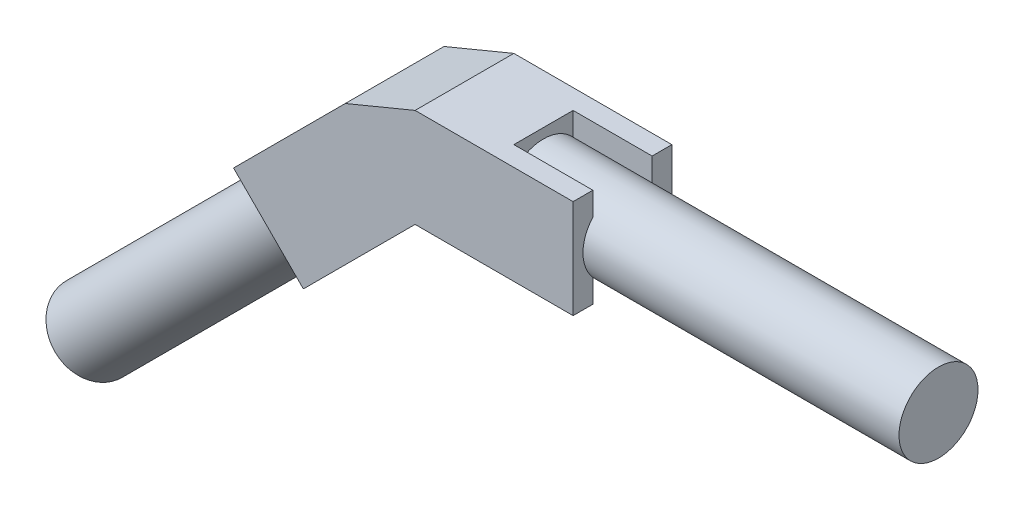
SolidWorks part; units mm, degrees
ref_plane "Front Plane" through (0, 0, 0) normal (0, 0, 1) x (1, 0, 0)
ref_plane "Top Plane" through (0, 0, 0) normal (0, 1, 0) x (1, 0, 0)
ref_plane "Right Plane" through (0, 0, 0) normal (1, 0, 0) x (0, 0, -1)
sketch "Sketch1" plane through (0, 0, 0) normal (1, 0, 0) x (0, 0, -1)
  circle A0 centre (0, 0) radius 12.7
  dimension "D1" = 25.4
extrude "Boss-Extrude1" add sketch "Sketch1" along normal blind 127
sketch "Sketch2" plane through (0, 0, 0) normal (-1, 0, 0) x (0, 0, 1)
  line L1 (-15.875, 15.875) -> (15.875, 15.875)
  line L2 (-15.875, 15.875) -> (-15.875, -15.875)
  line L3 (-15.875, -15.875) -> (15.875, -15.875)
  line L4 (15.875, 15.875) -> (15.875, -15.875)
  line L5 (-15.875, 15.875) -> (15.875, -15.875) construction
  line L6 (-15.875, -15.875) -> (15.875, 15.875) construction
  point P0 (0, 0)
  dimension "D1" = 31.75
  dimension "D2" = 31.75
extrude "Boss-Extrude2" add sketch "Sketch2" along normal blind 25.4
sketch "Sketch3" plane through (0, 0, 15.875) normal (0, 0, 1) x (1, 0, 0)
  line L1 (0, 15.875) -> (25.4, 15.875)
  line L2 (0, 15.875) -> (0, -15.875)
  line L3 (0, -15.875) -> (25.4, -15.875)
  line L4 (25.4, 15.875) -> (25.4, -15.875)
  dimension "D1" = 25.4
  dimension "D2" = 31.75
extrude "Boss-Extrude3" add sketch "Sketch3" against normal blind 6.35
sketch "Sketch4" plane through (0, 0, -15.875) normal (0, 0, -1) x (-1, 0, 0)
  line L1 (0, 15.875) -> (-25.4, 15.875)
  line L2 (0, 15.875) -> (0, -15.875)
  line L3 (0, -15.875) -> (-25.4, -15.875)
  line L4 (-25.4, 15.875) -> (-25.4, -15.875)
extrude "Boss-Extrude4" add sketch "Sketch4" against normal blind 6.35
ref_plane "Plane3" through (-20.6375, -20.6375, 0) normal (-0.7071, -0.7071, 0) x (0, 0, 1)
sketch "Sketch9" plane through (-20.6375, -20.6375, 0) normal (-0.7071, -0.7071, 0) x (0, 0, 1)
  line L1 (-15.875, 6.7352) -> (15.875, 6.7352)
  line L2 (-15.875, 6.7352) -> (-15.875, 38.4852)
  line L3 (-15.875, 38.4852) -> (15.875, 38.4852)
  line L4 (15.875, 6.7352) -> (15.875, 38.4852)
  dimension "D1" = 31.75
  dimension "D2" = 31.75
extrude "Boss-Extrude5" add sketch "Sketch9" along normal blind 25.4 separate body contours L3 L4 L1 L2
sketch "Sketch11" plane through (-38.598, -38.598, 0) normal (-0.7071, -0.7071, 0) x (0, 0, 1)
  line L0 (0, 38.4852) -> (0, 6.7352) construction
  line L1 (-15.875, 38.4852) -> (15.875, 38.4852) construction
  line L2 (-15.875, 6.7352) -> (15.875, 6.7352) construction
  line L3 (-15.875, 22.6102) -> (15.875, 22.6102) construction
  line L4 (-15.875, 6.7352) -> (-15.875, 38.4852) construction
  line L5 (15.875, 6.7352) -> (15.875, 38.4852) construction
  circle A0 centre (0, 22.6102) radius 12.7
  dimension "D1" = 25.4
extrude "Boss-Extrude6" add sketch "Sketch11" along normal blind 127
sketch "Sketch13" plane through (0, 0, 15.875) normal (0, 0, 1) x (1, 0, 0)
  line L0 (-43.3605, -33.8355) -> (-61.321, -51.796)
  line L1 (-61.321, -51.796) -> (-83.7717, -29.3454)
  line L4 (-83.7717, -29.3454) -> (-65.8112, -11.3849)
  line L5 (-65.8112, -11.3849) -> (-43.3605, -33.8355)
  dimension "D1" = 25.4
  dimension "D2" = 31.75
extrude "Boss-Extrude7" add sketch "Sketch13" against normal blind 6.35
sketch "Sketch14" plane through (0, 0, -15.875) normal (0, 0, -1) x (-1, 0, 0)
  line L0 (65.8112, -11.3849) -> (83.7717, -29.3454)
  line L1 (83.7717, -29.3454) -> (61.321, -51.796)
  line L2 (61.321, -51.796) -> (43.3605, -33.8355)
  line L3 (43.3605, -33.8355) -> (65.8112, -11.3849)
extrude "Boss-Extrude8" add sketch "Sketch14" against normal blind 6.35
sketch "Sketch15" plane through (0, 0, -15.875) normal (0, 0, -1) x (-1, 0, 0)
  line L0 (25.4, 15.875) -> (47.8506, 6.5756)
  line L1 (47.8506, 6.5756) -> (25.4, -15.875)
  line L2 (61.321, -51.796) -> (25.4, -15.875) construction
  line L3 (25.4, 15.875) -> (25.4, -15.875) construction
  line L4 (25.4, -15.875) -> (25.4, 15.875)
extrude "Boss-Extrude9" add sketch "Sketch15" against normal blind 31.75
